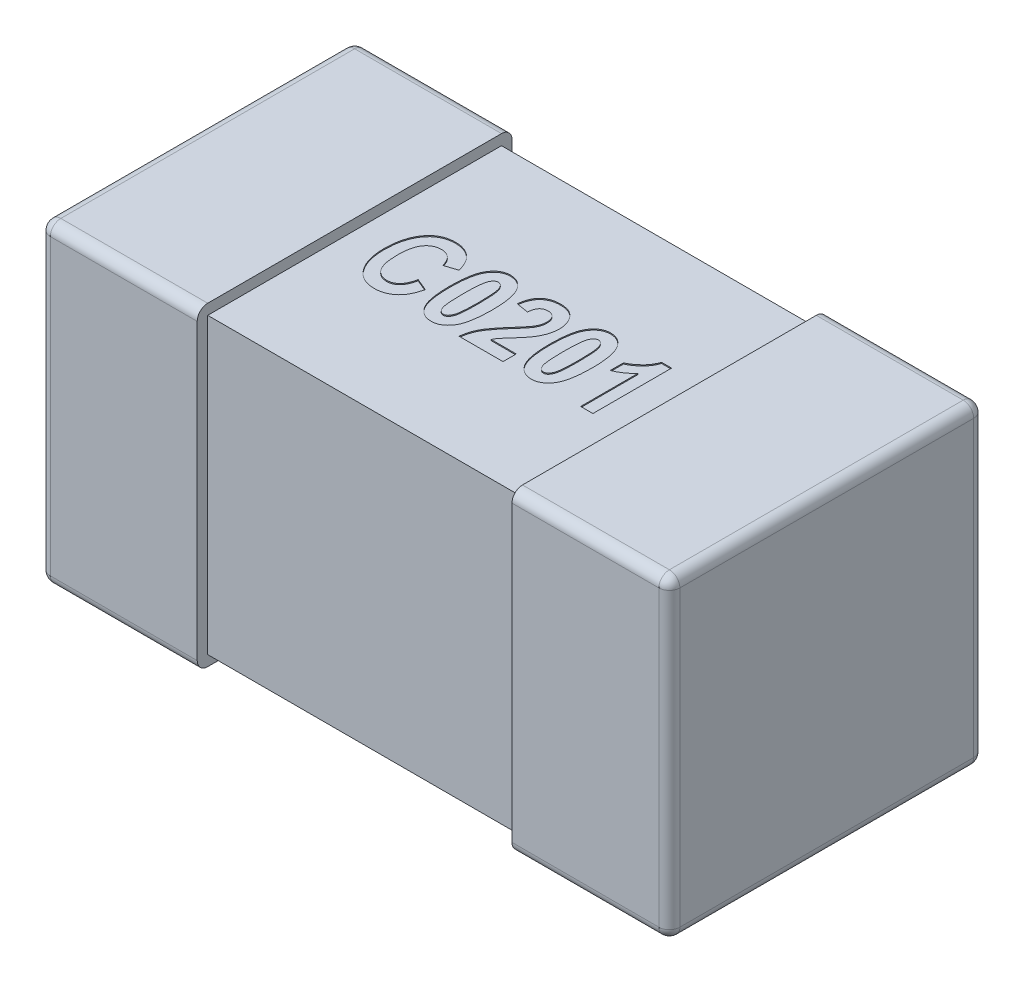
SolidWorks part; units mm, degrees
ref_plane "Front Plane" through (0, 0, 0) normal (0, 0, 1) x (1, 0, 0)
ref_plane "Top Plane" through (0, 0, 0) normal (0, 1, 0) x (1, 0, 0)
ref_plane "Right Plane" through (0, 0, 0) normal (1, 0, 0) x (0, 0, -1)
sketch "Sketch1" plane through (0, 0, 0) normal (0, 1, 0) x (1, 0, 0)
  line L0 (0, 0.15) -> (0, -0.15) construction
  line L1 (-0.3, 0) -> (0, 0) construction
  line L3 (-0.3, 0.15) -> (-0.15, 0.15)
  line L4 (-0.3, 0.15) -> (-0.3, -0.15)
  line L5 (-0.3, -0.15) -> (-0.15, -0.15)
  line L6 (-0.15, 0.15) -> (-0.15, -0.15)
  dimension "BANDWIDTH" = 0.15
  dimension "WIDTH" = 0.3
  dimension "LENGTH-HALF" = 0.3
extrude "THICKNESS" add sketch "Sketch1" along normal blind 0.3
fillet "Fillet1" radius 0.01 8 edges at (-0.3, 0, 0) (-0.225, 0, -0.15) (-0.3, 0.15, -0.15) (-0.225, 0, 0.15) (-0.3, 0.15, 0.15) (-0.3, 0.3, 0) (-0.225, 0.3, -0.15) (-0.225, 0.3, 0.15)
sketch "Sketch2" plane through (0, 0, 0) normal (1, 0, 0) x (0, 0, -1)
  line L0 (0, 0.3) -> (0, 0) construction
  line L1 (-0.14, 0.29) -> (0.14, 0.29)
  line L2 (-0.14, 0.29) -> (-0.14, 0.01)
  line L3 (-0.14, 0.01) -> (0.14, 0.01)
  line L4 (0.14, 0.29) -> (0.14, 0.01)
  line L5 (-0.14, 0.3) -> (0.14, 0.3) construction
  line L6 (-0.14, 0) -> (0.14, 0) construction
  line L7 (-0.15, 0.15) -> (0.15, 0.15) construction
  line L8 (-0.15, 0.29) -> (-0.15, 0.01) construction
  line L9 (0.15, 0.29) -> (0.15, 0.01) construction
  dimension "D1" = 0.01
  dimension "D2" = 0.01
extrude "Boss-Extrude2" add sketch "Sketch2" against normal up to surface (0.15 mm away) up to face at (-0.15, 0.15, 0)
mirror "Mirror3" about plane through (0, 0, 0) normal (1, 0, 0) of "Boss-Extrude2", "Fillet1", "THICKNESS"
sketch "Sketch3" plane through (0, 0.29, 0) normal (0, 1, 0) x (1, 0, 0)
  line L0 (-0.125, -0.0375) -> (0.125, -0.0375) construction
  line L1 (0, -0.165) -> (0, 0.165) construction
  line L2 (-0.165, 0) -> (0.165, 0) construction
  text T0 "<b>C0201</b>" font "Arial Narrow" height 0.075
  point P2 (0, -0.0375)
  dimension "D1" = 0.25
  dimension "D2" = 0.0375
extrude "Cut-Extrude1" cut sketch "Sketch3" against normal blind 0.001
